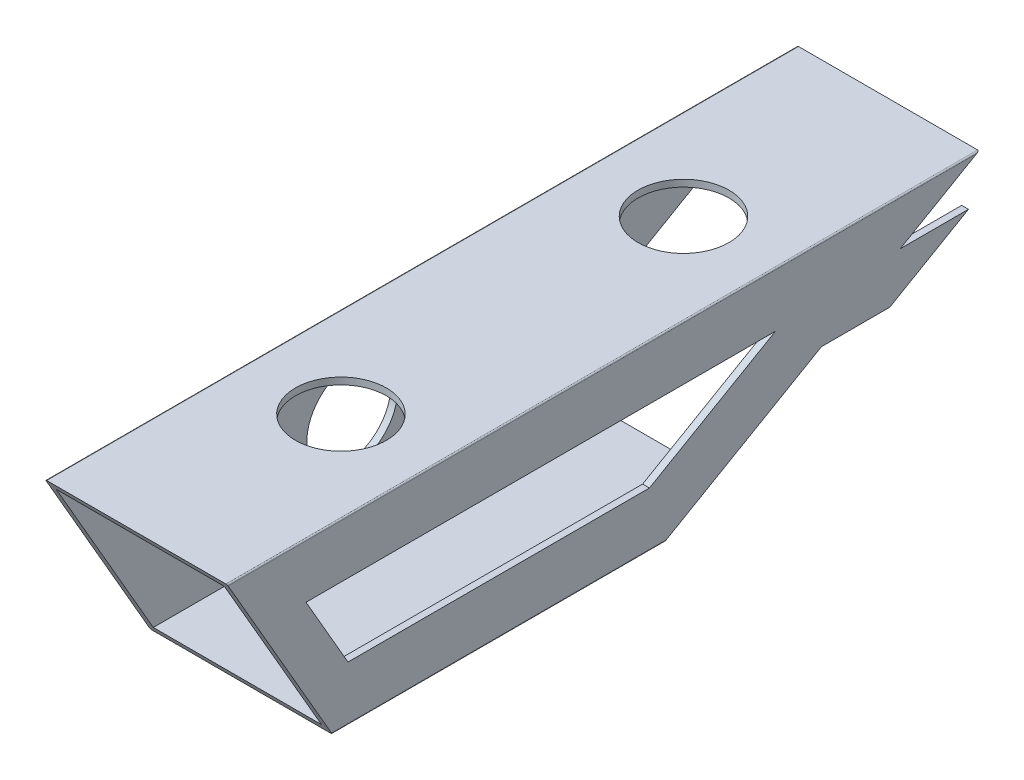
SolidWorks part; units mm, degrees
ref_plane "Front Plane" through (0, 0, 0) normal (0, 0, 1) x (1, 0, 0)
ref_plane "Top Plane" through (0, 0, 0) normal (0, 1, 0) x (1, 0, 0)
ref_plane "Right Plane" through (0, 0, 0) normal (1, 0, 0) x (0, 0, -1)
sketch "Sketch1" plane through (0, 0, 0) normal (0, 0, 1) x (1, 0, 0)
  line L0 (1.5, 1.5) -> (38.5, 1.5)
  line L1 (0.305, 0) -> (39.695, 0)
  line L2 (0, 0.305) -> (0, 39.695)
  line L3 (0.305, 40) -> (39.695, 40)
  line L4 (40, 0.305) -> (40, 39.695)
  line L5 (38.5, 1.5) -> (38.5, 38.5)
  line L6 (1.5, 38.5) -> (38.5, 38.5)
  line L7 (1.5, 1.5) -> (1.5, 38.5)
  arc A0 (0, 39.695) -> (0.305, 40) centre (0.305, 39.695) cw
  arc A1 (0.305, 0) -> (0, 0.305) centre (0.305, 0.305) cw
  arc A2 (39.695, 0) -> (40, 0.305) centre (39.695, 0.305) ccw
  arc A3 (39.695, 40) -> (40, 39.695) centre (39.695, 39.695) cw
  arc A4 (38.5, 1.5) -> (38.5, 1.5) centre (38.5, 1.5) ccw
  arc A5 (38.5, 38.5) -> (38.5, 38.5) centre (38.5, 38.5) cw
  arc A6 (1.5, 38.5) -> (1.5, 38.5) centre (1.5, 38.5) cw
  arc A7 (1.5, 1.5) -> (1.5, 1.5) centre (1.5, 1.5) cw
  point P9 (0, 0)
  dimension "D3" = 0.305
  dimension "D1" = 40
  dimension "D2" = 40
  dimension "D4" = 1.5
extrude "Boss-Extrude1" add sketch "Sketch1" along normal blind 165.35
sketch "Sketch2" plane through (40, 0, 0) normal (1, 0, 0) x (0, 0, -1)
  line L0 (0, 40) -> (-69.282, 0)
  line L1 (-165.35, 0) -> (0, 0) construction
  line L2 (-69.282, 0) -> (0, 0)
  line L3 (0, 0) -> (0, 40)
  line L4 (-165.35, 40) -> (-142.256, 0)
  line L5 (-142.256, 0) -> (-165.35, 0)
  line L6 (-165.35, 0) -> (-165.35, 40)
  dimension "D1" = 60
  dimension "D2" = 30
extrude "Cut-Extrude1" cut sketch "Sketch2" against normal blind 50
sketch "Sketch3" plane through (0, 0, 0) normal (-1, 0, 0) x (0, 0, 1)
  line L0 (69.282, 0) -> (52.282, 0)
  line L1 (52.282, 0) -> (52.282, 1.5)
  line L2 (52.282, 1.5) -> (66.684, 1.5)
  line L3 (0.5283, 39.695) -> (68.7537, 0.305) construction
  line L4 (66.684, 1.5) -> (69.282, 0)
  dimension "D1" = 1.5
  dimension "D2" = 17
extrude "Boss-Extrude2" add sketch "Sketch3" against normal blind 20 from offset 10 offset against normal yes
sketch "Sketch4" plane through (0, 0, 0) normal (-1, 0, 0) x (0, 0, 1)
  line L0 (2.3205, 30) -> (19.641, 20)
  line L1 (19.641, 20) -> (34.641, 20)
  line L2 (0.5283, 39.695) -> (68.7537, 0.305) construction
  line L3 (34.641, 20) -> (17.3205, 30)
  line L4 (17.3205, 30) -> (2.3205, 30)
  line L5 (165.35, 40) -> (0, 40) construction
  dimension "D1" = 10
  dimension "D2" = 10
  dimension "D3" = 15
extrude "Boss-Extrude3" add sketch "Sketch4" along normal blind 1.5 from offset 40 offset against normal yes
sketch "Sketch5" plane through (40, 0, 0) normal (1, 0, 0) x (0, 0, -1)
  line L0 (-44.7846, 28) -> (-72.4974, 12)
  line L1 (-72.4974, 12) -> (-138.7919, 12)
  line L2 (-138.7919, 12) -> (-148.0295, 28)
  line L3 (-148.0295, 28) -> (-44.7846, 28)
  line L4 (-34.641, 20) -> (-68.7537, 0.305) construction
  line L5 (-142.4321, 0.305) -> (-165.1739, 39.695) construction
  line L6 (-142.256, 0) -> (-69.282, 0) construction
  line L7 (-165.35, 40) -> (0, 40) construction
  dimension "D1" = 12
  dimension "D2" = 12
  dimension "D3" = 12
  dimension "D4" = 9
extrude "Cut-Extrude2" cut sketch "Sketch5" against normal blind 10
sketch "Sketch6" plane through (0, 40, 0) normal (0, 1, 0) x (1, 0, 0)
  line L0 (0.305, -82.675) -> (30.2575, -82.675) construction
  line L1 (0.305, -165.35) -> (0.305, 0) construction
  line L2 (39.695, -165.35) -> (0.305, -165.35) construction
  circle A0 centre (20, -120.35) radius 10
  circle A1 centre (20, -45) radius 10
  dimension "D1" = 20
  dimension "D2" = 45
extrude "Cut-Extrude3" cut sketch "Sketch6" against normal blind 10
sketch "Sketch7" plane through (1.5, 0, 0) normal (1, 0, 0) x (0, 0, -1)
  line L0 (-165.35, 40) -> (0, 40) construction
  circle A0 centre (-99.35, 20) radius 10
  dimension "D1" = 20
  dimension "D2" = 20
  dimension "D3" = 66
extrude "Cut-Extrude4" cut sketch "Sketch7" against normal blind 10
